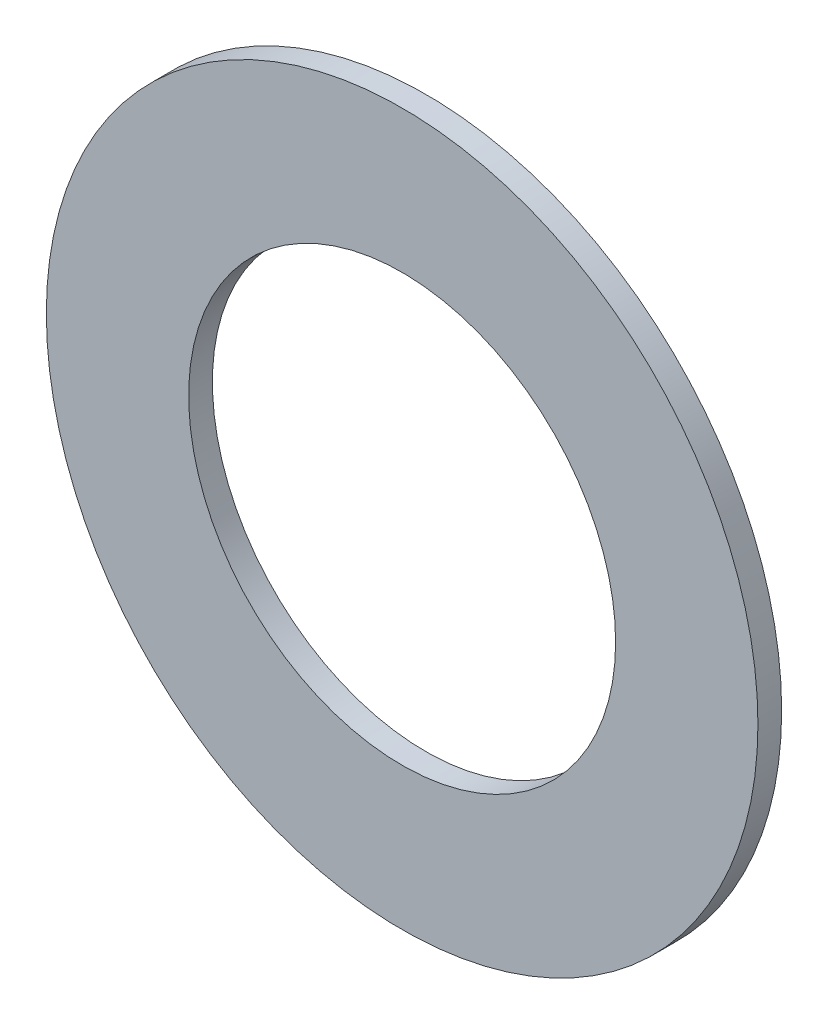
SolidWorks part; units mm, degrees
ref_plane "Front Plane" through (0, 0, 0) normal (0, 0, 1) x (1, 0, 0)
ref_plane "Top Plane" through (0, 0, 0) normal (0, 1, 0) x (1, 0, 0)
ref_plane "Right Plane" through (0, 0, 0) normal (1, 0, 0) x (0, 0, -1)
sketch "Sketch1" plane through (0, 0, 0) normal (0, 0, 1) x (1, 0, 0)
  circle A0 centre (0, 0) radius 3.75
  circle A1 centre (0, 0) radius 2.25
  dimension "D2" = 1.5
  dimension "D1" = 4.5
extrude "Boss-Extrude1" add sketch "Sketch1" along normal blind 0.25
